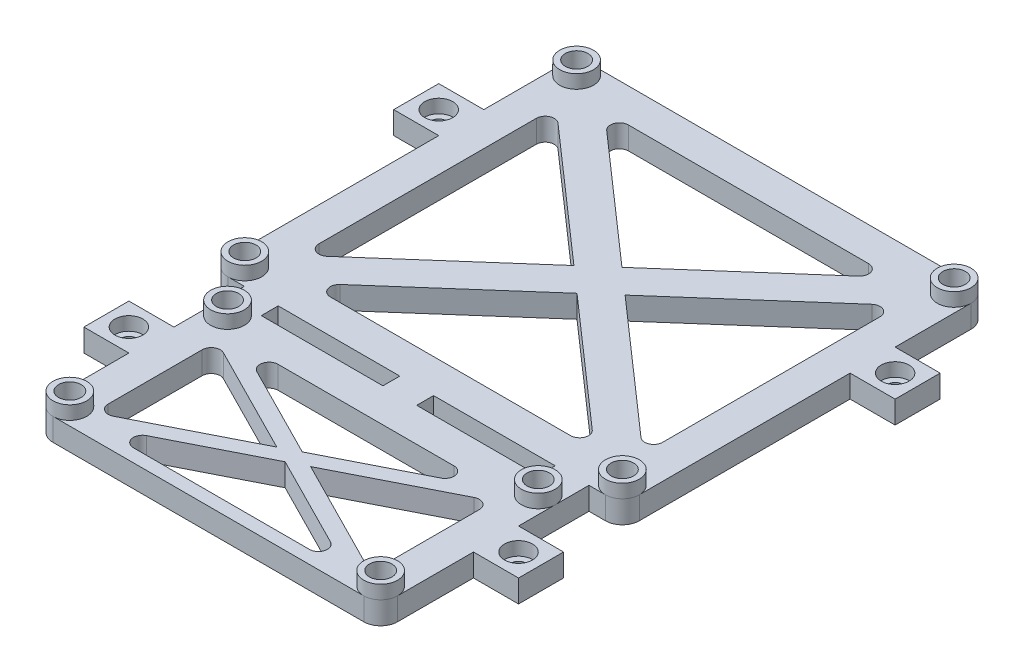
SolidWorks part; units mm, degrees
ref_plane "Front Plane" through (0, 0, 0) normal (0, 0, 1) x (1, 0, 0)
ref_plane "Top Plane" through (0, 0, 0) normal (0, 1, 0) x (1, 0, 0)
ref_plane "Right Plane" through (0, 0, 0) normal (1, 0, 0) x (0, 0, -1)
sketch "Sketch2" plane through (0, 0, 0) normal (0, 1, 0) x (1, 0, 0)
  line L0 (38.16, -28.5423) -> (5.6808, 0)
  line L1 (41.91, -36.83) -> (-41.91, -36.83) construction
  line L2 (41.91, -36.83) -> (41.91, 36.83) construction
  line L3 (41.91, 36.83) -> (-41.91, 36.83) construction
  line L4 (-41.91, -36.83) -> (-41.91, 36.83) construction
  line L5 (41.91, -36.83) -> (-41.91, 36.83) construction
  line L6 (41.91, 36.83) -> (-41.91, -36.83) construction
  line L7 (-34.5, -83.08) -> (34.5, -83.08) construction
  line L8 (-34.5, -83.08) -> (-34.5, -48.08) construction
  line L9 (-34.5, -48.08) -> (34.5, -48.08) construction
  line L10 (34.5, -83.08) -> (34.5, -48.08) construction
  line L11 (-34.5, -83.08) -> (34.5, -48.08) construction
  line L12 (-34.5, -48.08) -> (34.5, -83.08) construction
  line L13 (-38.16, -28.5423) -> (-38.16, 28.5423)
  line L14 (45.66, 40.58) -> (-45.66, 40.58)
  line L15 (45.66, -40.58) -> (45.66, 40.58)
  line L16 (-34.5, -48.08) -> (-34.5, -40.58) construction
  line L17 (38.16, 28.5423) -> (5.6808, 0)
  line L18 (45.66, -40.58) -> (38.25, -40.58)
  line L19 (-45.66, -40.58) -> (-45.66, 40.58)
  line L20 (31.9619, 33.08) -> (0, 4.9922)
  line L21 (0, -48.08) -> (0, -40.58) construction
  line L22 (31.9619, 33.08) -> (-31.9619, 33.08)
  line L23 (31.9619, -33.08) -> (0, -4.9922)
  line L24 (41.91, -40.58) -> (-41.91, -40.58) construction
  line L25 (-45.66, -36.83) -> (-45.66, 36.83) construction
  line L26 (45.66, -36.83) -> (45.66, 36.83) construction
  line L27 (41.91, 40.58) -> (-41.91, 40.58) construction
  line L28 (39.4346, -39.6469) -> (-44.3854, 34.0131) construction
  line L29 (34.5, -48.08) -> (34.5, -40.58) construction
  line L30 (-38.25, -86.83) -> (-38.25, -48.08)
  line L31 (-38.16, -36.83) -> (-38.16, 36.83) construction
  line L32 (-30.75, -44.33) -> (-3.75, -44.33)
  line L33 (-34.5, -44.33) -> (34.5, -44.33) construction
  line L34 (-5.6808, 0) -> (-38.16, -28.5423)
  line L35 (-32.8036, -86.4244) -> (36.1964, -51.4244) construction
  line L36 (-5.6808, 0) -> (-38.16, 28.5423)
  line L37 (0, 4.9922) -> (-31.9619, 33.08)
  line L38 (0, -4.9922) -> (-31.9619, -33.08)
  line L39 (31.9619, -33.08) -> (-31.9619, -33.08)
  line L40 (30.75, -83.08) -> (30.75, -48.08) construction
  line L41 (38.16, -28.5423) -> (38.16, 28.5423)
  line L42 (30.75, -81.5783) -> (30.75, -54.187)
  line L43 (30.75, -44.33) -> (30.75, -40.58)
  line L44 (-38.25, -48.08) -> (-38.25, -40.58)
  line L45 (-3.75, -44.33) -> (-3.75, -40.58)
  line L46 (-27.8967, -83.9354) -> (27.8967, -83.9354)
  line L47 (-27.8967, -51.83) -> (0, -65.9805)
  line L48 (-30.75, -54.187) -> (-3.75, -67.8827)
  line L49 (-27.8967, -83.9354) -> (0, -69.7849)
  line L50 (-38.25, -86.83) -> (38.25, -86.83)
  line L51 (38.25, -86.83) -> (38.25, -48.08)
  line L52 (38.25, -48.08) -> (38.25, -40.58)
  line L53 (-30.75, -44.33) -> (-30.75, -40.58)
  line L54 (3.75, -44.33) -> (3.75, -40.58)
  line L55 (-38.25, -83.08) -> (-38.25, -48.08) construction
  line L56 (-34.5, -86.83) -> (34.5, -86.83) construction
  line L57 (38.25, -83.08) -> (38.25, -48.08) construction
  line L58 (-30.75, -81.5783) -> (-3.75, -67.8827)
  line L59 (-30.75, -81.5783) -> (-30.75, -54.187)
  line L60 (-36.1964, -51.4244) -> (32.8036, -86.4244) construction
  line L61 (-3.75, -48.08) -> (-3.75, -40.58) construction
  line L62 (0, -69.7849) -> (27.8967, -83.9354)
  line L63 (3.75, -67.8827) -> (30.75, -54.187)
  line L64 (0, -65.9805) -> (27.8967, -51.83)
  line L65 (3.75, -67.8827) -> (30.75, -81.5783)
  line L66 (-30.75, -48.08) -> (-30.75, -40.58) construction
  line L67 (-27.8967, -51.83) -> (27.8967, -51.83)
  line L68 (3.75, -44.33) -> (30.75, -44.33)
  line L69 (3.75, -48.08) -> (3.75, -40.58) construction
  line L70 (30.75, -40.58) -> (3.75, -40.58)
  line L71 (30.75, -48.08) -> (30.75, -40.58) construction
  line L72 (-3.75, -40.58) -> (-30.75, -40.58)
  line L73 (-38.25, -40.58) -> (-45.66, -40.58)
  circle A0 centre (-41.91, 36.83) radius 2.5
  circle A1 centre (41.91, 36.83) radius 2.5
  circle A2 centre (-41.91, -36.83) radius 2.5
  circle A3 centre (41.91, -36.83) radius 2.5
  circle A4 centre (-34.5, -48.08) radius 2.5
  circle A5 centre (-34.5, -83.08) radius 2.5
  circle A6 centre (34.5, -83.08) radius 2.5
  circle A7 centre (34.5, -48.08) radius 2.5
  point P0 (0, 0)
  point P6 (0, -65.58)
  point P93 (0, 0)
  point P94 (18.8176, -60.2397)
  dimension "D15" = 5
  dimension "D1" = 83.82
  dimension "D2" = 73.66
  dimension "D3" = 69
  dimension "D4" = 35
  dimension "D7" = 3.75
  dimension "D8" = 3.75
  dimension "D9" = 7.5
  dimension "D10" = 7.5
  dimension "D13" = 7.5
  dimension "D14" = 3.8043
  dimension "D16" = 3.75
  dimension "D5" = 3.75
  dimension "D6" = 3.75
  dimension "D11" = 3.75
  dimension "D12" = 3.75
extrude "Boss-Extrude2" add sketch "Sketch2" along normal blind 5 contours L73 L44 L30 L50 L51 L52 L18 L15 L14 L19 L72 L45 L32 L53 L70 L43 L68 L54 L65 L63 L42 L41 L0 L17 L36 L34 L13 L20 L37 L22 L23 L39 L38 L58 L59 L48 L49 L62 L46 L47 L67
sketch "Sketch3" plane through (0, 5, 0) normal (0, 1, 0) x (1, 0, 0)
  line L0 (-45.66, -40.58) -> (-45.66, 40.58) construction
  line L1 (45.66, 40.58) -> (-45.66, 40.58) construction
  line L2 (45.66, -40.58) -> (45.66, 40.58) construction
  line L3 (45.66, -40.58) -> (38.25, -40.58) construction
  line L4 (38.25, -86.83) -> (38.25, -40.58) construction
  line L5 (-38.25, -86.83) -> (38.25, -86.83) construction
  line L6 (-38.25, -86.83) -> (-38.25, -40.58) construction
  circle A0 centre (-41.91, 36.83) radius 3.75
  circle A1 centre (41.91, 36.83) radius 3.75
  circle A2 centre (41.91, -36.83) radius 3.75
  circle A3 centre (-41.91, -36.83) radius 3.75
  circle A4 centre (-34.5, -48.08) radius 3.75
  circle A5 centre (-34.5, -83.08) radius 3.75
  circle A6 centre (34.5, -83.08) radius 3.75
  circle A7 centre (34.5, -48.08) radius 3.75
  circle A8 centre (-34.5, -83.08) radius 2.5
  circle A9 centre (34.5, -83.08) radius 2.5
  circle A10 centre (34.5, -48.08) radius 2.5
  circle A11 centre (-34.5, -48.08) radius 2.5
  circle A12 centre (-41.91, -36.83) radius 2.5
  circle A13 centre (41.91, -36.83) radius 2.5
  circle A14 centre (41.91, 36.83) radius 2.5
  circle A15 centre (-41.91, 36.83) radius 2.5
  circle A16 centre (-41.91, 36.83) radius 2.5 construction
  circle A17 centre (41.91, 36.83) radius 2.5 construction
  circle A18 centre (41.91, -36.83) radius 2.5 construction
  circle A19 centre (-41.91, -36.83) radius 2.5 construction
  circle A20 centre (-34.5, -48.08) radius 2.5 construction
  circle A21 centre (34.5, -48.08) radius 2.5 construction
  circle A22 centre (34.5, -83.08) radius 2.5 construction
  circle A23 centre (-34.5, -83.08) radius 2.5 construction
extrude "Boss-Extrude3" add sketch "Sketch3" along normal blind 3
fillet "Fillet1" radius 3.75 6 edges at (-45.66, 2.5, -40.58) (38.25, 2.5, 86.83) (-38.25, 2.5, 86.83) (-45.66, 2.5, 40.58) (45.66, 2.5, 40.58) (45.66, 2.5, -40.58)
sketch "Sketch4" plane through (0, 0, 0) normal (0, -1, 0) x (1, 0, 0)
  line L0 (-45.66, 36.83) -> (-45.66, -36.83) construction
  line L1 (-45.66, -19.975) -> (-55.66, -19.975)
  line L2 (-45.66, -19.975) -> (-45.66, -9.975)
  line L3 (-45.66, -9.975) -> (-55.66, -9.975)
  line L4 (-55.66, -19.975) -> (-55.66, -9.975)
  line L5 (45.66, 36.83) -> (45.66, -36.83) construction
  line L6 (45.66, -19.975) -> (55.66, -19.975)
  line L7 (45.66, -19.975) -> (45.66, -9.975)
  line L8 (45.66, -9.975) -> (55.66, -9.975)
  line L9 (55.66, -19.975) -> (55.66, -9.975)
  line L10 (-38.25, 83.08) -> (-38.25, 40.58) construction
  line L11 (-38.25, 56.225) -> (-48.25, 56.225)
  line L12 (-38.25, 56.225) -> (-38.25, 66.225)
  line L13 (-38.25, 66.225) -> (-48.25, 66.225)
  line L14 (-48.25, 56.225) -> (-48.25, 66.225)
  line L15 (38.25, 83.08) -> (38.25, 40.58) construction
  line L16 (38.25, 66.225) -> (48.25, 66.225)
  line L17 (38.25, 66.225) -> (38.25, 56.225)
  line L18 (38.25, 56.225) -> (48.25, 56.225)
  line L19 (48.25, 66.225) -> (48.25, 56.225)
  point P13 (-45.66, -14.975)
  point P15 (45.66, -14.975)
  point P28 (-38.25, 61.225)
  point P29 (38.25, 61.225)
  dimension "D1" = 10
  dimension "D2" = 14.975
  dimension "D3" = 61.225
extrude "Boss-Extrude4" add sketch "Sketch4" against normal up to surface (5 mm away) up to face at (-17.25, 5, 42.455)
sketch "Sketch5" plane through (0, 5, 0) normal (0, 1, 0) x (1, 0, 0)
  line L0 (-45.66, 19.975) -> (-55.66, 9.975) construction
  line L2 (-38.25, -56.225) -> (-48.25, -66.225) construction
  line L4 (55.66, 19.975) -> (45.66, 9.975) construction
  line L7 (48.25, -56.225) -> (38.25, -66.225) construction
  point P27 (-50.66, 14.975)
  point P29 (-43.25, -61.225)
  point P31 (43.25, -61.225)
  point P33 (50.66, 14.975)
hole_wizard "CBORE for M3 SHCS1" positions "Sketch5" profile "Sketch6" counterbore size "M3" standard "ANSI Metric" end condition through all
sketch "Sketch6" plane through (50.66, 5, -14.975) normal (1, 0, 0) x (0, 0, 1)
  line L0 (0, 0) -> (0, 5)
  line L1 (0, 5) -> (1.7, 5)
  line L3 (1.7, 5) -> (1.7, 3)
  line L4 (1.7, 3) -> (3.1, 3)
  line L5 (3.1, 3) -> (3.1, 0)
  line L7 (3.1, 0) -> (0, 0)
  line L11 (0, -6.35) -> (0, 107.95) construction
  dimension "Thru Hole Dia." = 3.4
  dimension "Thru Hole Depth" = 5
  dimension "C'Bore Dia." = 6.2
  dimension "C'Bore Depth" = 3
sketch "Sketch8" plane through (0, 0, 0) normal (0, -1, 0) x (1, 0, 0)
  circle A0 centre (-34.5, 83.08) radius 2.5
  circle A1 centre (34.5, 83.08) radius 2.5
  circle A2 centre (34.5, 48.08) radius 2.5
  circle A3 centre (41.91, 36.83) radius 2.5
  circle A4 centre (41.91, -36.83) radius 2.5
  circle A5 centre (-41.91, -36.83) radius 2.5
  circle A6 centre (-41.91, 36.83) radius 2.5
  circle A8 centre (-34.5, 48.08) radius 2.5
  circle A9 centre (-34.5, 83.08) radius 2.5 construction
extrude "Boss-Extrude5" add sketch "Sketch8" against normal blind 4
fillet "Fillet2" radius 2 16 edges at (27.8967, 2.5, 51.83) (30.75, 2.5, 54.187) (30.75, 2.5, 81.5783) (27.8967, 2.5, 83.9354) (-27.8967, 2.5, 83.9354) (-30.75, 2.5, 81.5783) (-30.75, 2.5, 54.187) (-27.8967, 2.5, 51.83) (-31.9619, 2.5, -33.08) (31.9619, 2.5, -33.08) (38.16, 2.5, -28.5423) (38.16, 2.5, 28.5423) (31.9619, 2.5, 33.08) (-31.9619, 2.5, 33.08) (-38.16, 2.5, 28.5423) (-38.16, 2.5, -28.5423)
